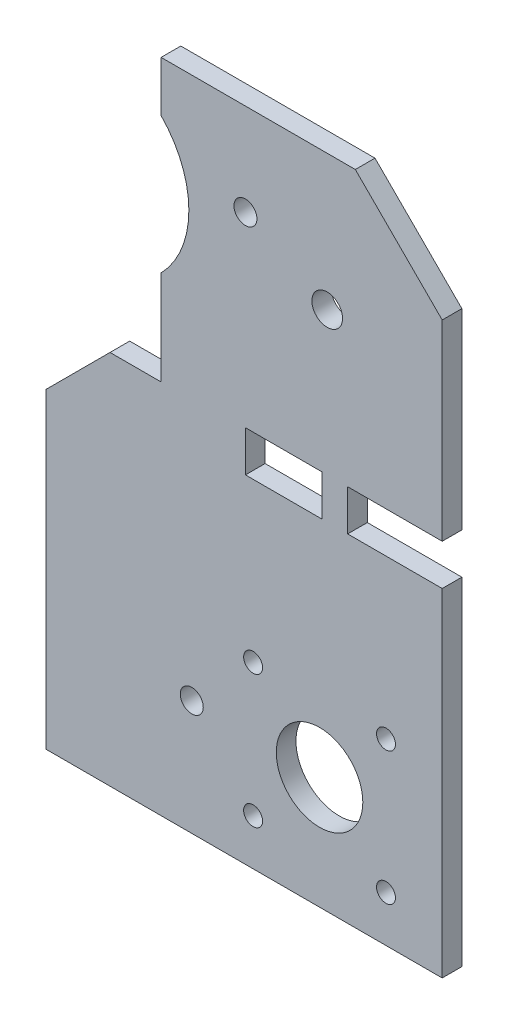
SolidWorks part; units mm, degrees
ref_plane "Front Plane" through (0, 0, 0) normal (0, 0, 1) x (1, 0, 0)
ref_plane "Top Plane" through (0, 0, 0) normal (0, 1, 0) x (1, 0, 0)
ref_plane "Right Plane" through (0, 0, 0) normal (1, 0, 0) x (0, 0, -1)
sketch "Sketch1" plane through (0, 0, 0) normal (0, 0, 1) x (1, 0, 0)
  line L1 (-13.3232, 13.2625) -> (141.6768, 13.2625)
  line L2 (-13.3232, 13.2625) -> (-13.3232, -243.7375)
  line L3 (-13.3232, -243.7375) -> (141.6768, -243.7375)
  line L4 (141.6768, 13.2625) -> (141.6768, -243.7375)
  dimension "D1" = 155
  dimension "D2" = 257
extrude "Boss-Extrude1" add sketch "Sketch1" along normal blind 7.7
chamfer "Chamfer1" distance 34 angle 45 1 edges at (141.6768, 13.2625, 3.85)
sketch "Sketch2" plane through (0, 0, 7.7) normal (0, 0, 1) x (1, 0, 0)
  line L0 (141.6768, -243.7375) -> (141.6768, -20.7375) construction
  line L1 (141.6768, -95.7375) -> (104.6768, -95.7375)
  line L2 (141.6768, -95.7375) -> (141.6768, -111.7375)
  line L3 (141.6768, -111.7375) -> (104.6768, -111.7375)
  line L4 (104.6768, -95.7375) -> (104.6768, -111.7375)
  line L5 (-13.3232, -243.7375) -> (141.6768, -243.7375) construction
  line L6 (107.6768, 13.2625) -> (-13.3232, 13.2625) construction
  line L7 (-13.3232, 13.2625) -> (-13.3232, -243.7375) construction
  circle A0 centre (64.6768, -22.7375) radius 4.5
  circle A1 centre (43.6768, -198.7375) radius 4.5
  point P12 (0, 0)
  point P14 (0, 0)
  dimension "D6" = 9
  dimension "D9" = 9
  dimension "D1" = 132
  dimension "D2" = 16
  dimension "D3" = 37
  dimension "D4" = 77
  dimension "D5" = 36
  dimension "D7" = 57
  dimension "D8" = 45
extrude "Cut-Extrude1" cut sketch "Sketch2" against normal blind 10
sketch "Sketch3" plane through (0, 0, 7.7) normal (0, 0, 1) x (1, 0, 0)
  circle A0 centre (4.4291, -33.1194) radius 38.1099
extrude "Cut-Extrude2" cut sketch "Sketch3" against normal blind 10
sketch "Sketch4" plane through (0, 0, 7.7) normal (0, 0, 1) x (1, 0, 0)
  line L7 (31.6768, 13.2625) -> (31.6768, -96.7375)
  line L8 (107.6768, 13.2625) -> (-13.3232, 13.2625) construction
  line L9 (141.6768, -95.7375) -> (141.6768, -20.7375) construction
  line L12 (-67.6978, -122.4359) -> (-69.5539, 22.0734)
  line L13 (-69.5539, 22.0734) -> (23.8985, 29.8094)
  line L14 (23.8985, 29.8094) -> (31.6768, 13.2625)
  line L15 (31.6768, -96.7375) -> (11.6768, -96.7375)
  line L16 (11.6768, -96.7375) -> (-13.3232, -121.7375)
  line L17 (-13.3232, -66.842) -> (-13.3232, -243.7375) construction
  line L18 (-13.3232, -121.7375) -> (-67.6978, -122.4359)
  dimension "D1" = 110
  dimension "D2" = 110
  dimension "D3" = 25
  dimension "D4" = 25
extrude "Cut-Extrude3" cut sketch "Sketch4" against normal blind 10
sketch "Sketch5" plane through (0, 0, 7.7) normal (0, 0, 1) x (1, 0, 0)
  line L0 (-13.3232, -243.7375) -> (141.6768, -243.7375) construction
  line L1 (141.6768, -243.7375) -> (141.6768, -111.7375) construction
  circle A0 centre (93.6768, -199.7375) radius 16.9351
  dimension "D1" = 44
  dimension "D2" = 48
extrude "Cut-Extrude4" cut sketch "Sketch5" against normal blind 10
sketch "Sketch6" plane through (0, 0, 7.7) normal (0, 0, 1) x (1, 0, 0)
  circle A0 centre (67.6768, -225.7375) radius 3.7055
  circle A1 centre (93.6768, -199.7375) radius 16.9351 construction
  dimension "D1" = 26
  dimension "D2" = 26
extrude "Cut-Extrude5" cut sketch "Sketch6" against normal blind 10
pattern_linear "LPattern1" count 2 spacing 52 along (0, 1, 0) count 2 spacing 52 along (1, 0, 0) of "Cut-Extrude5"
sketch "Sketch7" plane through (0, 0, 7.7) normal (0, 0, 1) x (1, 0, 0)
  line L0 (107.6768, 13.2625) -> (31.6768, 13.2625) construction
  line L1 (141.6768, -95.7375) -> (141.6768, -20.7375) construction
  circle A0 centre (96.6768, -39.7375) radius 6
  point P2 (90.1679, -38.7253)
  dimension "D3" = 12
  dimension "D1" = 53
  dimension "D2" = 45
extrude "Cut-Extrude6" cut sketch "Sketch7" against normal blind 10
sketch "Sketch8" plane through (0, 0, 7.7) normal (0, 0, 1) x (1, 0, 0)
  line L0 (141.6768, -95.7375) -> (104.6768, -95.7375) construction
  line L1 (94.6768, -95.7375) -> (64.6768, -95.7375)
  line L2 (94.6768, -95.7375) -> (94.6768, -111.7375)
  line L3 (94.6768, -111.7375) -> (64.6768, -111.7375)
  line L4 (64.6768, -95.7375) -> (64.6768, -111.7375)
  line L5 (104.6768, -111.7375) -> (141.6768, -111.7375) construction
  line L6 (104.6768, -95.7375) -> (104.6768, -111.7375) construction
  dimension "D1" = 10
  dimension "D2" = 30
extrude "Cut-Extrude7" cut sketch "Sketch8" against normal blind 10
